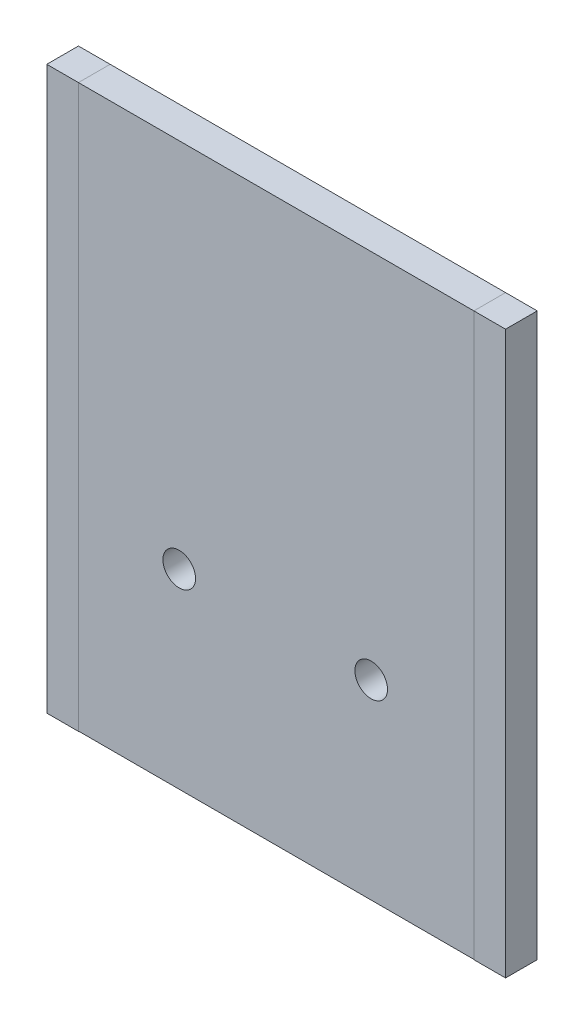
SolidWorks part; units mm, degrees
ref_plane "前基準面" through (0, 0, 0) normal (0, 0, 1) x (1, 0, 0)
ref_plane "上基準面" through (0, 0, 0) normal (0, 1, 0) x (1, 0, 0)
ref_plane "右基準面" through (0, 0, 0) normal (1, 0, 0) x (0, 0, -1)
sketch "草圖1" plane through (0, 0, 0) normal (0, 0, 1) x (1, 0, 0)
  line L0 (1.2262, 28.739) -> (1.2262, 10.1035) construction
  line L2 (21.9262, 28.739) -> (21.9262, -28.6267)
  line L3 (21.9262, -28.6267) -> (-19.2738, -28.6267)
  line L4 (-19.2738, 28.739) -> (-19.2738, -28.6267)
  line L7 (-19.2738, 28.739) -> (-19.2738, 29.889)
  line L8 (-19.2738, 29.889) -> (21.9262, 29.889)
  line L9 (21.9262, 28.739) -> (21.9262, 29.889)
  line L10 (-19.2738, 29.889) -> (-22.5738, 29.889)
  line L11 (-19.2738, 29.889) -> (-19.2738, -28.6267)
  line L12 (-19.2738, -28.6267) -> (-22.5738, -28.6267)
  line L13 (-22.5738, 29.889) -> (-22.5738, -28.6267)
  circle A0 centre (11.2262, -8.761) radius 1.7
  circle A1 centre (-8.7738, -8.761) radius 1.7
  dimension "D1" = 41.2
  dimension "D6" = 1.15
extrude "填料-伸長1" add sketch "草圖1" against normal blind 3.3 contours L2 L3 L4 L7 L8 L9 | A0 | A1
sketch "草圖2" plane through (0, 0, 0) normal (0, 0, 1) x (1, 0, 0)
  line L1 (21.9262, 29.889) -> (25.2262, 29.889)
  line L2 (21.9262, 29.889) -> (21.9262, -28.6555)
  line L3 (21.9262, -28.6555) -> (25.2262, -28.6555)
  line L4 (25.2262, 29.889) -> (25.2262, -28.6555)
  line L5 (-19.2738, 29.889) -> (-22.5738, 29.889)
  line L6 (-19.2738, 29.889) -> (-19.2738, -28.6555)
  line L7 (-19.2738, -28.6555) -> (-22.5738, -28.6555)
  line L8 (-22.5738, 29.889) -> (-22.5738, -28.6555)
  point P10 (0, 0)
  dimension "D1" = 3.3
  dimension "D2" = 3.3
extrude "填料-伸長2" add sketch "草圖2" against normal blind 3.3 separate body contours L4 L1 L2 L3 | L6 L5 L8 L7
